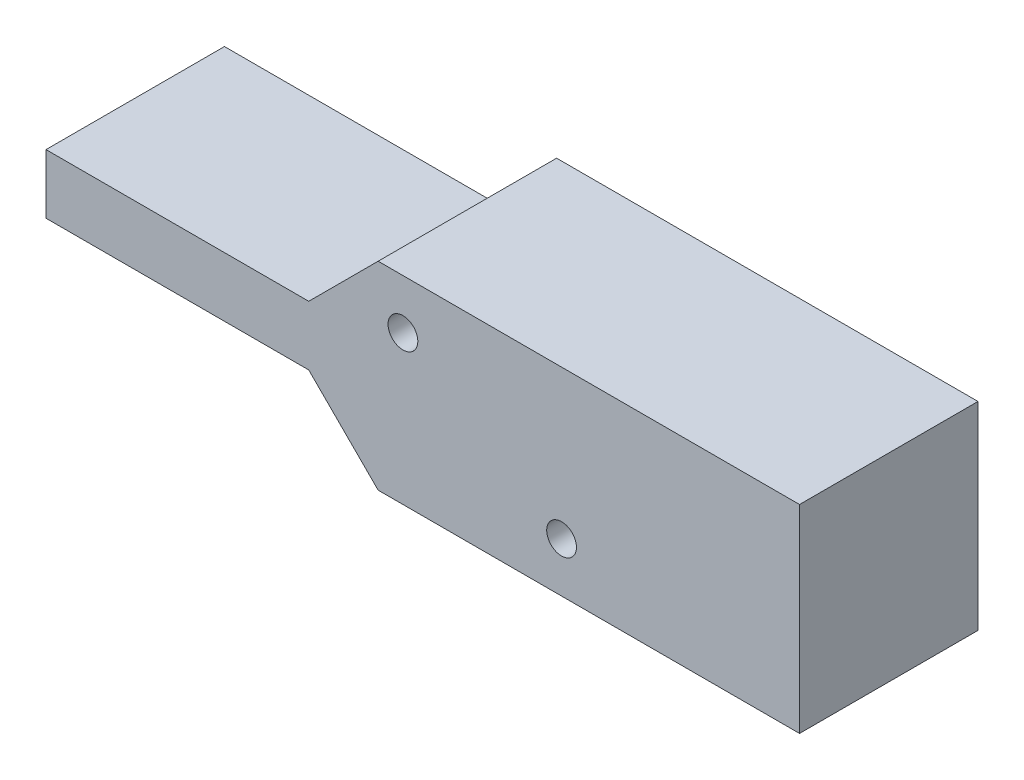
SolidWorks part; units mm, degrees
ref_plane "Ebene vorne" through (0, 0, 0) normal (0, 0, 1) x (1, 0, 0)
ref_plane "Ebene oben" through (0, 0, 0) normal (0, 1, 0) x (1, 0, 0)
ref_plane "Ebene rechts" through (0, 0, 0) normal (1, 0, 0) x (0, 0, -1)
sketch "Skizze1" plane through (0, 0, 0) normal (0, 0, 1) x (1, 0, 0)
  line L0 (-76, -7) -> (-76, -13)
  line L1 (-76, -13) -> (-49.5, -13)
  line L2 (-49.5, -13) -> (-42.5, -20)
  line L3 (-42.5, -20) -> (0, -20)
  line L4 (0, -20) -> (0, 0)
  line L5 (0, 0) -> (-42.5, 0)
  line L6 (-42.5, 0) -> (-49.5, -7)
  line L7 (-49.5, -7) -> (-76, -7)
  circle A0 centre (-40, -5) radius 1.5
  circle A1 centre (-24, -15) radius 1.5
  dimension "D11" = 3
  dimension "D12" = 3
  dimension "D1" = 20
  dimension "D2" = 0
  dimension "D3" = 6
  dimension "D4" = 7
  dimension "D5" = 42.5
  dimension "D6" = 0
  dimension "D7" = 7
  dimension "D8" = 26.5
  dimension "D9" = 0
  dimension "D10" = 0
  dimension "D13" = 16
  dimension "D14" = 10
  dimension "D15" = 5
  dimension "D16" = 24
extrude "Aufsatz-Linear austragen1" add sketch "Skizze1" along normal blind 18
